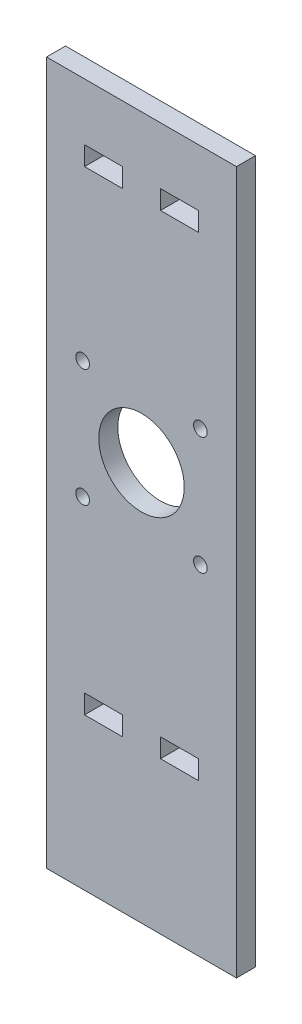
SolidWorks part; units mm, degrees
ref_plane "Front Plane" through (0, 0, 0) normal (0, 0, 1) x (1, 0, 0)
ref_plane "Top Plane" through (0, 0, 0) normal (0, 1, 0) x (1, 0, 0)
ref_plane "Right Plane" through (0, 0, 0) normal (1, 0, 0) x (0, 0, -1)
sketch "Sketch1" plane through (0, 0, 0) normal (0, 0, 1) x (1, 0, 0)
  line L0 (25, 185) -> (25, 0) construction
  line L1 (0, 0) -> (50, 0)
  line L2 (0, 0) -> (0, 185)
  line L3 (0, 185) -> (50, 185)
  line L4 (50, 0) -> (50, 185)
  line L5 (10, 170) -> (20, 170)
  line L6 (10, 170) -> (10, 165)
  line L7 (10, 165) -> (20, 165)
  line L8 (20, 170) -> (20, 165)
  line L9 (10, 45) -> (20, 45)
  line L10 (10, 45) -> (10, 40)
  line L11 (10, 40) -> (20, 40)
  line L12 (20, 45) -> (20, 40)
  line L13 (30, 45) -> (30, 40)
  line L14 (40, 40) -> (30, 40)
  line L15 (40, 45) -> (30, 45)
  line L16 (40, 45) -> (40, 40)
  line L17 (30, 170) -> (30, 165)
  line L18 (40, 165) -> (30, 165)
  line L19 (40, 170) -> (40, 165)
  line L20 (40, 170) -> (30, 170)
  circle A0 centre (25, 105) radius 11.25
  circle A1 centre (9.5, 120.5) radius 1.8
  circle A2 centre (9.5, 89.5) radius 1.8
  circle A3 centre (40.5, 89.5) radius 1.8
  circle A4 centre (40.5, 120.5) radius 1.8
  point P13 (10, 42.5)
  point P14 (20, 42.5)
  dimension "D11" = 25
  dimension "D13" = 15.5
  dimension "D15" = 15.5
  dimension "D1" = 50
  dimension "D2" = 185
  dimension "D3" = 40
  dimension "D4" = 5
  dimension "D5" = 10
  dimension "D6" = 10
  dimension "D7" = 5
  dimension "D8" = 15
  dimension "D9" = 10
  dimension "D10" = 10
  dimension "D12" = 60
  dimension "D14" = 15.5
  dimension "D16" = 31
extrude "Boss-Extrude1" add sketch "Sketch1" along normal blind 5
